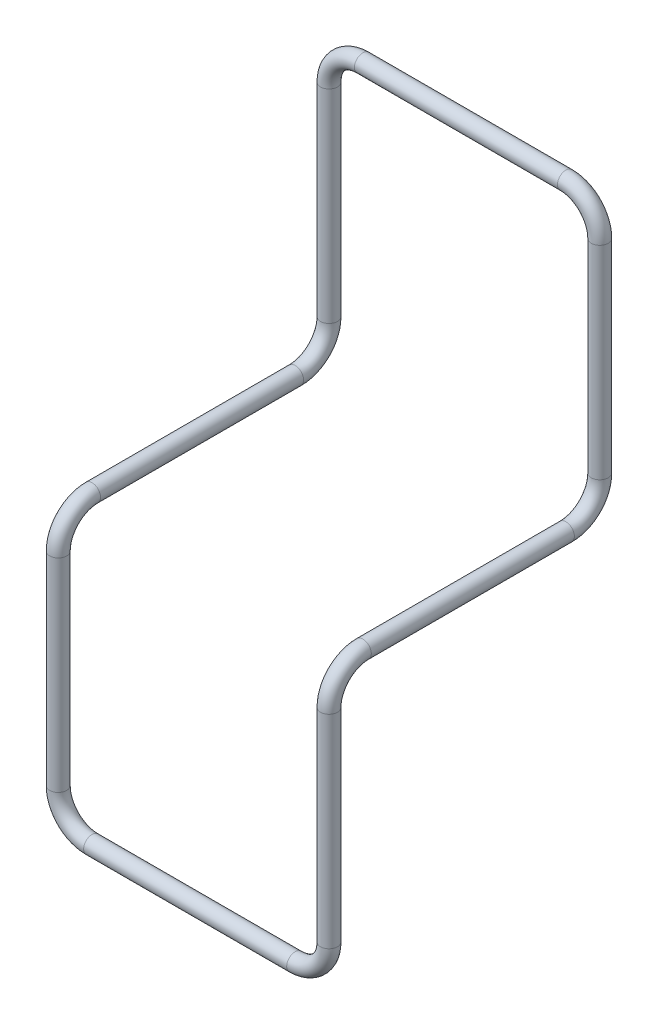
SolidWorks part; units mm, degrees
ref_plane "Front Plane" through (0, 0, 0) normal (0, 0, 1) x (1, 0, 0)
ref_plane "Top Plane" through (0, 0, 0) normal (0, 1, 0) x (1, 0, 0)
ref_plane "Right Plane" through (0, 0, 0) normal (1, 0, 0) x (0, 0, -1)
sketch3d "3DSketch3"
  line L0 (0, -6.35, 0) -> (0, -44.45, 0)
  line L1 (0, -50.8, 6.35) -> (0, -50.8, 44.45)
  line L2 (0, -57.15, 50.8) -> (0, -95.25, 50.8)
  line L3 (6.35, -101.6, 50.8) -> (44.45, -101.6, 50.8)
  line L4 (50.8, -95.25, 50.8) -> (50.8, -57.15, 50.8)
  line L5 (50.8, -50.8, 44.45) -> (50.8, -50.8, 6.35)
  line L6 (50.8, -44.45, 0) -> (50.8, -6.35, 0)
  line L7 (44.45, 0, 0) -> (6.35, 0, 0)
  arc A0 (50.8, -6.35, 0) -> (44.45, 0, 0) centre (44.45, -6.35, 0) ccw
  arc A1 (50.8, -50.8, 6.35) -> (50.8, -44.45, 0) centre (50.8, -44.45, 6.35) ccw
  arc A2 (44.45, -101.6, 50.8) -> (50.8, -95.25, 50.8) centre (44.45, -95.25, 50.8) ccw
  arc A3 (0, -95.25, 50.8) -> (6.35, -101.6, 50.8) centre (6.35, -95.25, 50.8) ccw
  arc A4 (50.8, -57.15, 50.8) -> (50.8, -50.8, 44.45) centre (50.8, -57.15, 44.45) ccw
  arc A5 (0, -50.8, 44.45) -> (0, -57.15, 50.8) centre (0, -57.15, 44.45) ccw
  arc A6 (0, -44.45, 0) -> (0, -50.8, 6.35) centre (0, -44.45, 6.35) ccw
  arc A7 (0, -6.35, 0) -> (6.35, 0, 0) centre (6.35, -6.35, 0) ccw
  point P11 (50.8, 0, 0)
  point P12 (44.45, -6.35, 6.35)
  point P15 (50.8, -50.8, 0)
  point P16 (57.15, -44.45, 6.35)
  point P19 (50.8, -101.6, 50.8)
  point P20 (44.45, -95.25, 57.15)
  point P23 (0, -101.6, 50.8)
  point P24 (6.35, -95.25, 57.15)
  point P27 (50.8, -50.8, 50.8)
  point P28 (44.45, -57.15, 44.45)
  point P31 (0, -50.8, 50.8)
  point P32 (6.35, -57.15, 44.45)
  point P35 (0, -50.8, 0)
  point P36 (-6.35, -44.45, 6.35)
  point P39 (0, 0, 0)
  point P40 (6.35, -6.35, -6.35)
  dimension "D1" = 6.35
  dimension "D2" = 50.8
  dimension "D3" = 50.8
  dimension "D4" = 50.8
  dimension "D5" = 50.8
  dimension "D6" = 50.8
  dimension "D7" = 50.8
  dimension "D8" = 50.8
ref_plane "Plane1" through (6.35, 0, 0) normal (1, 0, 0) x (0, 0, -1)
sketch "Sketch2" plane through (6.35, 0, 0) normal (1, 0, 0) x (0, 0, -1)
  circle A0 centre (0, 0) radius 1.5875
  dimension "D1" = 3.175
sweep "Sweep1" add profiles "Sketch2" path "3DSketch3"
